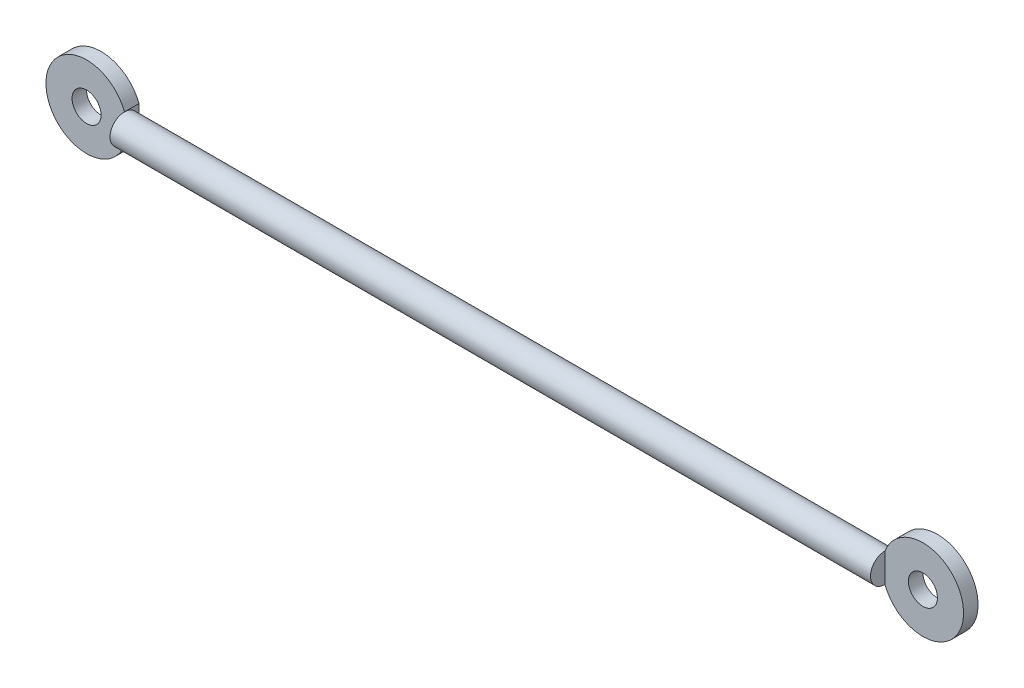
SolidWorks part; units mm, degrees
ref_plane "Front Plane" through (0, 0, 0) normal (0, 0, 1) x (1, 0, 0)
ref_plane "Top Plane" through (0, 0, 0) normal (0, 1, 0) x (1, 0, 0)
ref_plane "Right Plane" through (0, 0, 0) normal (1, 0, 0) x (0, 0, -1)
sketch "Sketch1" plane through (0, 0, 0) normal (0, 0, 1) x (1, 0, 0)
  line L0 (-65.5, 0) -> (65.5, 0)
  point P3 (0, 0)
  dimension "D1" = 131
revolve "Revolve-Thin1" add sketch "Sketch1" angle 360 about L0 wall 2.5
sketch "Sketch3" plane through (0, 0, 0) normal (0, 0, 1) x (1, 0, 0)
  line L0 (65.5, 2.5) -> (65.5, -2.5)
  line L1 (-65.5, -2.5) -> (-65.5, 2.5)
  arc A0 (65.5, 2.5) -> (65.5, -2.5) centre (72.0383, 0) cw
  arc A1 (-65.5, 2.5) -> (-65.5, -2.5) centre (-72.0383, 0) ccw
  circle A2 centre (-72.0383, 0) radius 2.5
  circle A3 centre (72.0383, 0) radius 2.5
  dimension "D1" = 7
  dimension "D2" = 5
extrude "Boss-Extrude2" add sketch "Sketch3" against normal blind 2.5
